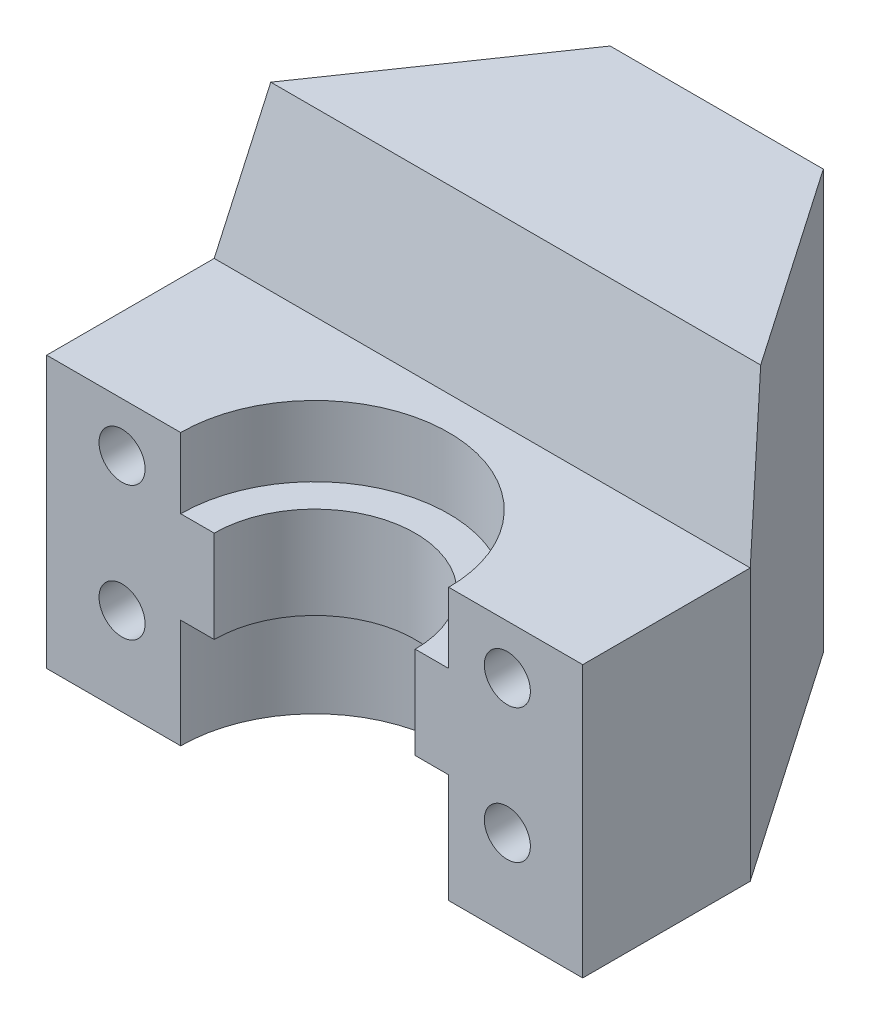
SolidWorks part; units mm, degrees
material "PLA"
ref_plane "Front Plane" through (0, 0, 0) normal (0, 0, 1) x (1, 0, 0)
ref_plane "Top Plane" through (0, 0, 0) normal (0, 1, 0) x (1, 0, 0)
ref_plane "Right Plane" through (0, 0, 0) normal (1, 0, 0) x (0, 0, -1)
sketch "Sketch1" plane through (0, 0, 0) normal (1, 0, 0) x (0, 0, -1)
  line L0 (0, 20) -> (12, 20) construction
  line L1 (0, 0) -> (12, 0)
  line L2 (0, 0) -> (0, 25)
  line L3 (0, 25) -> (12, 25)
  line L4 (12, 0) -> (12, 25)
  line L5 (0, 5) -> (12, 5) construction
  dimension "D1" = 15
  dimension "D2" = 12
  dimension "D3" = 25
  dimension "D4" = 5
extrude "Boss-Extrude1" add sketch "Sketch1" along normal mid plane 32 contours L4 L3 L2 L1
sketch "Sketch2" plane through (0, 0, 0) normal (0, 1, 0) x (1, 0, 0)
  line L0 (0, 0) -> (0, -2) construction
  line L1 (-16, -12) -> (16, -12)
  line L2 (-16, -12) -> (-16, -2)
  line L3 (-16, -2) -> (16, -2)
  line L4 (16, -12) -> (16, -2)
  line L5 (16, 0) -> (16, 12) construction
  dimension "D1" = 2
  dimension "D3" = 10
extrude "Boss-Extrude2" add sketch "Sketch2" along normal blind 16.2 separate body
sketch "Sketch3" plane through (16, 0, 0) normal (1, 0, 0) x (0, 0, -1)
  line L1 (-2, 0) -> (-2, 16.2) construction
  line L7 (0, 25) -> (0, 0) construction
  line L9 (-2, 0) -> (-2, 16.2)
  line L15 (0, 25) -> (0, 0)
  line L16 (0, 25) -> (-2, 16.2)
  line L17 (-2, 0) -> (0, 0)
extrude "Boss-Extrude3" add sketch "Sketch3" against normal up to surface (32 mm away) up to face at (-16, 8.1, 7)
hole_wizard "M5x0.8 Tapped Hole1" positions "Sketch7" profile "Sketch6" tap size "M5x0.8" standard "ANSI Metric"
sketch "Sketch7" plane through (0, 0, -12) normal (0, 0, -1) x (-1, 0, 0)
  line L0 (-16, 0) -> (16, 0) construction
  point P0 (0, 20)
  point P2 (0, 5)
  dimension "D1" = 15
  dimension "D2" = 5
sketch "Sketch6" plane through (0, 20, -12) normal (1, 0, 0) x (0, 1, 0)
  line L0 (0, 0) -> (0, 10.2618)
  line L1 (0, 10.2618) -> (2.1, 9)
  line L2 (2.1, 9) -> (2.1, 0)
  line L5 (2.1, 0) -> (0, 0)
  line L10 (0, 10.2618) -> (-2.1, 9) construction
  line L11 (0, -6.35) -> (0, 107.95) construction
  dimension "Tap Drill Dia." = 4.2
  dimension "Tap Drill Depth" = 9
  dimension "Drill Angle" = 118
cosmetic thread "Hole Thread1" parameters "D1"=4.2, "D2"=5
cosmetic thread "Hole Thread2" parameters "D1"=4.2, "D2"=5
sketch "Sketch9" plane through (0, 0, 0) normal (1, 0, 0) x (0, 0, -1)
  line L0 (-12, 16.2) -> (-4, 16.2)
  line L1 (-12, 16.2) -> (-12, 0) construction
  line L2 (-4, 16.2) -> (-4, 12)
  line L3 (-4, 12) -> (-6, 12)
  line L4 (-6, 12) -> (-6, 6.5)
  line L5 (-6, 6.5) -> (-4, 6.5)
  line L6 (-4, 6.5) -> (-4, 0)
  line L7 (-12, 0) -> (12, 0) construction
  line L8 (-4, 0) -> (-12, 0)
  line L9 (-12, 0) -> (-12, 16.2)
  line L10 (-12, 16.2) -> (-2, 16.2) construction
  dimension "D1" = 6
  dimension "D2" = 8
  dimension "D3" = 8
  dimension "D4" = 6.5
  dimension "D5" = 5.5
revolve "Cut-Revolve1" cut sketch "Sketch9" angle 360 about L9
sketch "Sketch10" plane through (0, 25, 0) normal (0, 1, 0) x (1, 0, 0)
  line L5 (16, -2) -> (16, 0) construction
  line L6 (-16, -2) -> (-6.3625, 12)
  line L7 (16, 12) -> (-16, 12) construction
  line L8 (-6.3625, 12) -> (-16, 12)
  line L9 (-16, 12) -> (-16, -2)
  line L10 (16, 12) -> (6.3625, 12)
  line L11 (16, -2) -> (16, 0)
  line L12 (6.3625, 12) -> (16, -2)
  line L13 (16, 12) -> (16, -2)
  line L14 (0, 0) -> (0, 12) construction
  line L15 (16, 0) -> (-16, 0) construction
  line M4 (-16, 12) -> (-16, 0)
  line M5 (-16, 0) -> (16, 0)
  line M6 (16, 0) -> (16, 12)
  line M7 (16, 12) -> (-16, 12)
  dimension "D1" = 12.725
extrude "Cut-Extrude2" cut sketch "Sketch10" against normal up to next contours L12 M7 M5 M6 | L12 L11 M5 | L6 M5 M7 M4 | L9 L6 M5
hole_wizard "M3x0.5 Tapped Hole1" positions "Sketch12" profile "Sketch11" tap size "M3x0.5" standard "ANSI Metric"
sketch "Sketch12" plane through (0, 0, 12) normal (0, 0, 1) x (1, 0, 0)
  line L0 (0, 0) -> (0, 16.2) construction
  line L1 (8, 16.2) -> (-8, 16.2) construction
  line L4 (-11.5, 13.25) -> (-11.5, 5.25) construction
  line L7 (-11.5, 9.25) -> (0, 9.25) construction
  line L10 (-6, 6.5) -> (-6, 12) construction
  point P0 (-11.5, 13.25)
  point P2 (11.5, 13.25)
  point P7 (-11.5, 5.25)
  point P8 (11.5, 5.25)
  point P36 (-6, 9.25)
  dimension "D1" = 8
  dimension "D2" = 23
sketch "Sketch11" plane through (-11.5, 13.25, 12) normal (1, 0, 0) x (0, -1, 0)
  line L0 (0, 0) -> (0, 12.8262)
  line L1 (0, 12.8262) -> (1.375, 12)
  line L2 (1.375, 12) -> (1.375, 0)
  line L5 (1.375, 0) -> (0, 0)
  line L10 (0, 12.8262) -> (-1.375, 12) construction
  line L11 (0, -6.35) -> (0, 107.95) construction
  dimension "Tap Drill Dia." = 2.75
  dimension "Tap Drill Depth" = 12
  dimension "Drill Angle" = 118
cosmetic thread "Hole Thread3" parameters "D1"=6, "D2"=3
cosmetic thread "Hole Thread4" parameters "D1"=6, "D2"=3
cosmetic thread "Hole Thread5" parameters "D1"=6, "D2"=3
cosmetic thread "Hole Thread6" parameters "D1"=6, "D2"=3
